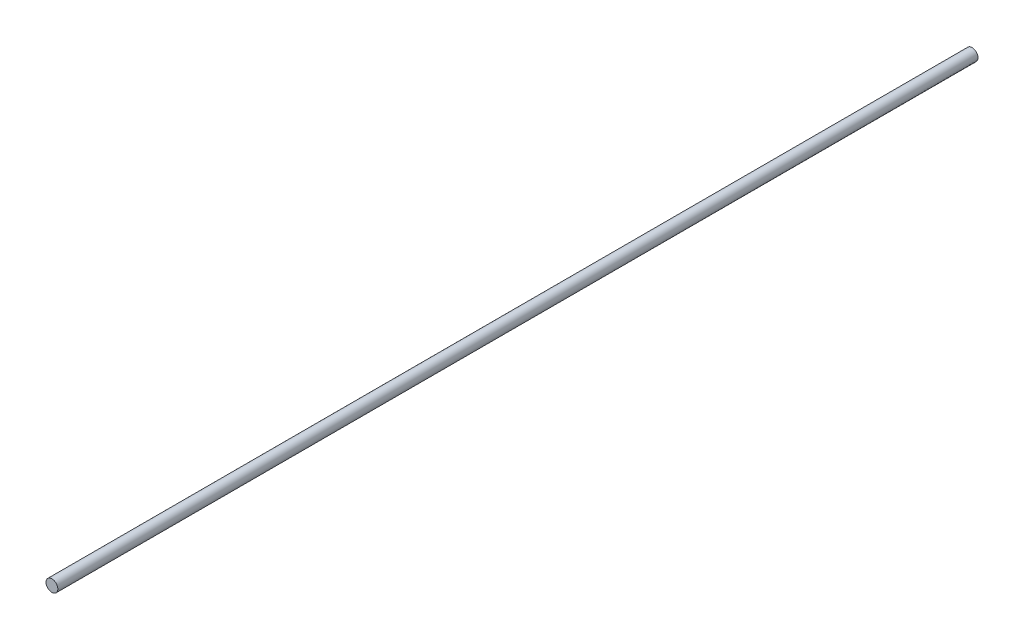
SolidWorks part; units mm, degrees
ref_plane "前视基准面" through (0, 0, 0) normal (0, 0, 1) x (1, 0, 0)
ref_plane "上视基准面" through (0, 0, 0) normal (0, 1, 0) x (1, 0, 0)
ref_plane "右视基准面" through (0, 0, 0) normal (1, 0, 0) x (0, 0, -1)
sketch "草图1" plane through (0, 0, 0) normal (0, 0, 1) x (1, 0, 0)
  circle A0 centre (0, 0) radius 0.45
  dimension "D1" = 0.9
extrude "凸台-拉伸1" add sketch "草图1" along normal blind 70
